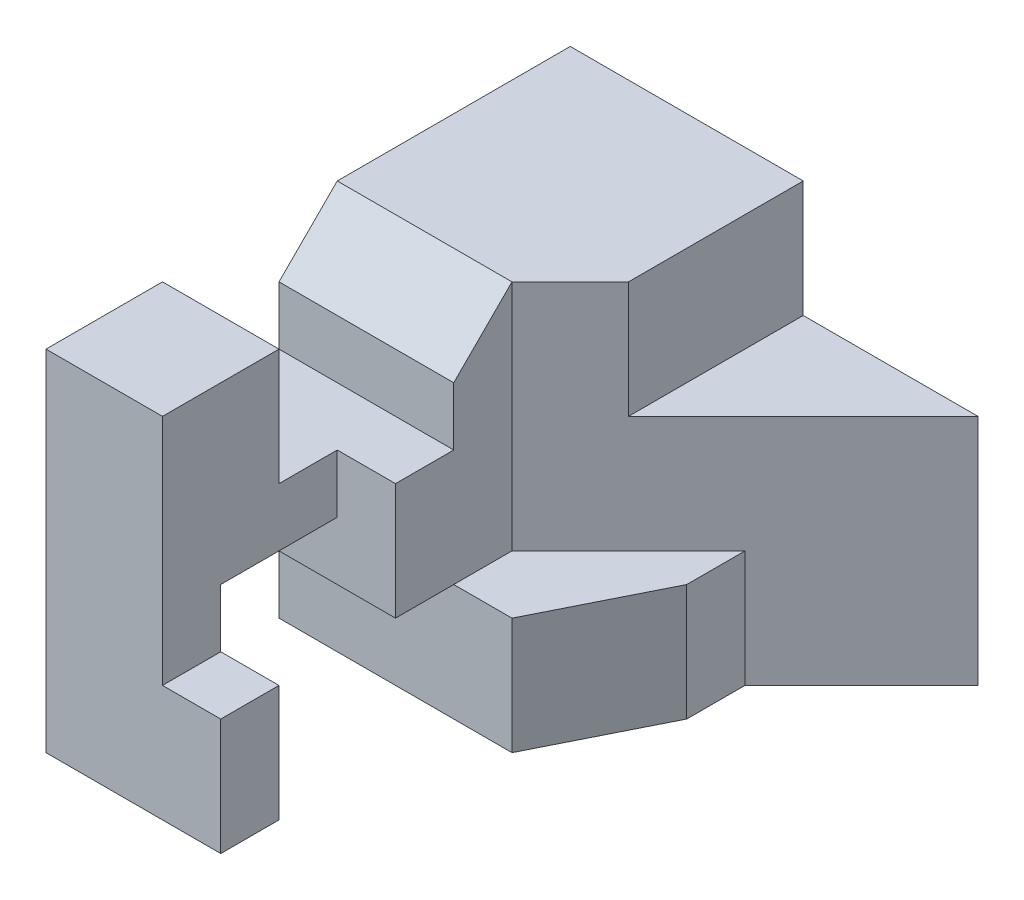
SolidWorks part; units mm, degrees
ref_plane "Front Plane" through (0, 0, 0) normal (0, 0, 1) x (1, 0, 0)
ref_plane "Top Plane" through (0, 0, 0) normal (0, 1, 0) x (1, 0, 0)
ref_plane "Right Plane" through (0, 0, 0) normal (1, 0, 0) x (0, 0, -1)
sketch "Sketch1" plane through (0, 0, 0) normal (0, 0, 1) x (1, 0, 0)
  line L1 (3.5, -3) -> (-3.5, -3)
  line L2 (3.5, -3) -> (3.5, 3)
  line L3 (3.5, 3) -> (-3.5, 3)
  line L4 (-3.5, -3) -> (-3.5, 3)
  line L5 (3.5, -3) -> (-3.5, 3) construction
  line L6 (3.5, 3) -> (-3.5, -3) construction
  point P0 (0, 0)
  dimension "D1" = 7
  dimension "D2" = 6
extrude "Boss-Extrude1" add sketch "Sketch1" along normal blind 9
sketch "Sketch2" plane through (0, 3, 0) normal (0, 1, 0) x (1, 0, 0)
  line L0 (3.5, 0) -> (0.5, 0)
  line L1 (3.5, 0) -> (-3.5, 0) construction
  line L2 (0.5, 0) -> (0.5, -3)
  line L3 (0.5, -3) -> (3.5, 0)
  dimension "D1" = 3
  dimension "D2" = 3
extrude "Cut-Extrude1" cut sketch "Sketch2" against normal blind 2
sketch "Sketch3" plane through (0, 3, 0) normal (0, 1, 0) x (1, 0, 0)
  line L0 (3.5, 0) -> (0.5, -3)
  line L1 (0.5, -3) -> (0.5, -9)
  line L2 (3.5, -9) -> (-3.5, -9) construction
  line L3 (0.5, -9) -> (3.5, -9)
  line L4 (3.5, -9) -> (3.5, 0)
extrude "Cut-Extrude3" cut sketch "Sketch3" against normal blind 4
sketch "Sketch4" plane through (0, 3, 0) normal (0, 1, 0) x (1, 0, 0)
  line L0 (3.5, 0) -> (1.5, -2)
  line L1 (0.5, -3) -> (3.5, 0) construction
  line L2 (1.5, -2) -> (1.5, -3)
  line L3 (1.5, -3) -> (0.5, -5)
  line L4 (0.5, 0) -> (0.5, -9) construction
  line L5 (0.5, -5) -> (0.5, -9)
  line L6 (0.5, -9) -> (3.5, -9)
  line L7 (3.5, -9) -> (3.5, 0)
  dimension "D1" = 1
  dimension "D2" = 1
  dimension "D3" = 4
extrude "Cut-Extrude4" cut sketch "Sketch4" against normal through all
sketch "Sketch5" plane through (0.5, 0, 0) normal (1, 0, 0) x (0, 0, -1)
  line L0 (-8, -3) -> (-8, -1)
  line L1 (-5, -3) -> (-9, -3) construction
  line L2 (-8, -1) -> (-5, -1)
  line L3 (-5, -1) -> (-5, -3)
  line L4 (-5, -3) -> (-8, -3)
  dimension "D1" = 2
  dimension "D2" = 1
extrude "Cut-Extrude5" cut sketch "Sketch5" against normal through all
sketch "Sketch7" plane through (0, 3, 0) normal (0, 1, 0) x (1, 0, 0)
  line L0 (0.5, -3) -> (-0.5, -4)
  line L1 (0.5, 0) -> (0.5, -9) construction
  line L2 (-0.5, -4) -> (-0.5, -9)
  line L3 (0.5, -9) -> (-3.5, -9) construction
  line L4 (-0.5, -9) -> (0.5, -9)
  line L5 (0.5, -9) -> (0.5, -3)
  line L6 (-3.5, -9) -> (-3.5, 0) construction
  line L7 (0.5, 0) -> (-3.5, 0) construction
  dimension "D1" = 3
  dimension "D2" = 3
  dimension "D3" = 4
extrude "Cut-Extrude8" cut sketch "Sketch7" against normal blind 4
sketch "Sketch8" plane through (-0.5, 0, 0) normal (1, 0, 0) x (0, 0, -1)
  line L0 (-4, 3) -> (-5, 2)
  line L1 (-5, 2) -> (-5, 1)
  line L2 (-5, 1) -> (-7, 1)
  line L3 (-7, 1) -> (-7, 3)
  line L4 (-4, 3) -> (-9, 3) construction
  line L5 (-7, 3) -> (-4, 3)
  dimension "D1" = 3
  dimension "D2" = 2
  dimension "D3" = 1
  dimension "D4" = 2
extrude "Cut-Extrude9" cut sketch "Sketch8" against normal through all
sketch "Sketch11" plane through (-0.5, 0, 0) normal (1, 0, 0) x (0, 0, -1)
  line L0 (-8, -1) -> (-8, 0)
  line L1 (-8, 0) -> (-6, 0)
  line L2 (-6, 0) -> (-6, -1)
  line L3 (-5, -1) -> (-8, -1) construction
  line L4 (-6, -1) -> (-8, -1)
  dimension "D1" = 2
extrude "Cut-Extrude12" cut sketch "Sketch11" against normal through all
sketch "Sketch12" plane through (-0.5, 0, 0) normal (1, 0, 0) x (0, 0, -1)
  line L0 (-9, 3) -> (-7, 3)
  line L1 (-7, 3) -> (-7, 1)
  line L2 (-7, 1) -> (-6, 1)
  line L3 (-7, 1) -> (-5, 1) construction
  line L4 (-6, 1) -> (-6, 0)
  line L5 (-6, 0) -> (-8, 0)
  line L6 (-8, 0) -> (-8, -1)
  line L7 (-9, -1) -> (-8, -1) construction
  line L8 (-8, -1) -> (-8, -3) construction
  line L9 (-8, -1) -> (-9, -1)
  line L10 (-9, -1) -> (-9, 3)
extrude "Cut-Extrude13" cut sketch "Sketch12" against normal blind 1
sketch "Sketch13" plane through (0, -1, 0) normal (0, 1, 0) x (1, 0, 0)
  line L0 (0.5, -8) -> (-0.5, -8)
  line L1 (-1.5, -8) -> (0.5, -8) construction
  line L2 (-0.5, -8) -> (-0.5, -9)
  line L3 (-1.5, -9) -> (0.5, -9) construction
  line L4 (-0.5, -9) -> (0.5, -9)
  line L5 (0.5, -9) -> (0.5, -8)
extrude "Cut-Extrude14" cut sketch "Sketch13" against normal through all
